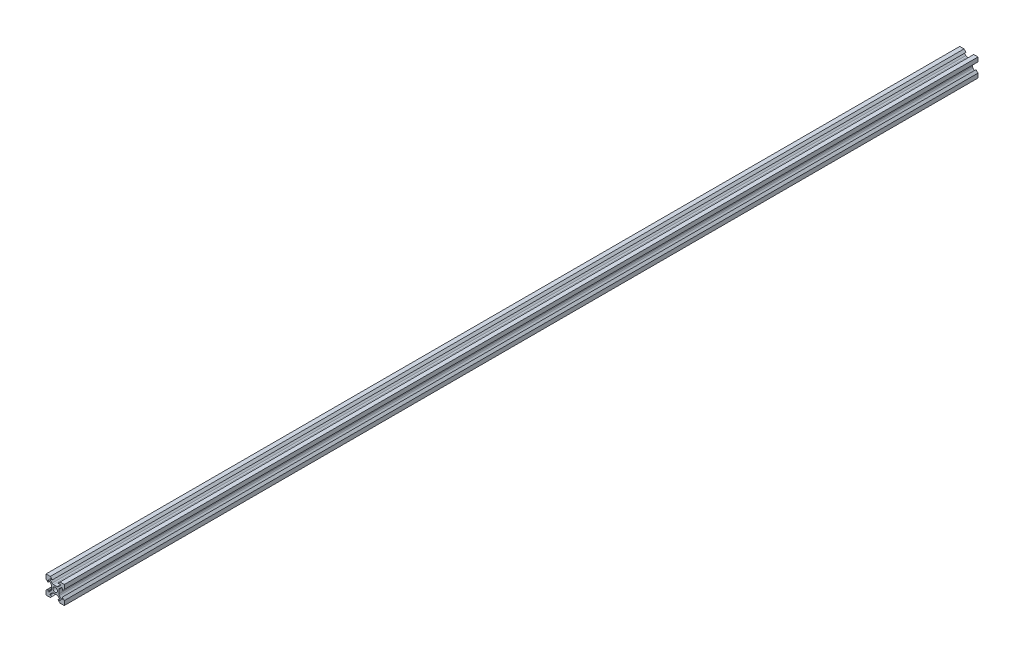
SolidWorks part; units mm, degrees
ref_plane "Front Plane" through (0, 0, 0) normal (0, 0, 1) x (1, 0, 0)
ref_plane "Top Plane" through (0, 0, 0) normal (0, 1, 0) x (1, 0, 0)
ref_plane "Right Plane" through (0, 0, 0) normal (1, 0, 0) x (0, 0, -1)
sketch "Sketch1" plane through (0, 0, 0) normal (0, 0, 1) x (1, 0, 0)
  line L0 (0, -10) -> (0, 10) construction
  line L1 (-10, 10) -> (10, 10) construction
  line L2 (-10, 10) -> (-10, -10) construction
  line L3 (-10, -10) -> (10, -10) construction
  line L4 (10, 10) -> (10, -10) construction
  line L5 (-10, 10) -> (10, -10) construction
  line L6 (-10, -10) -> (10, 10) construction
  line L7 (-10, 0) -> (10, 0) construction
  line L8 (-4, 0) -> (-4, 1.8988)
  line L9 (-4.5858, 3.313) -> (-6.8263, 5.5536)
  line L10 (-7.1799, 5.7) -> (-7.3, 5.7)
  line L11 (-7.8, 5.2) -> (-7.8, 3.1)
  line L12 (-7.8, 3.1) -> (-10, 5.3)
  line L13 (-10, 5.3) -> (-10, 10)
  line L14 (0, 4) -> (-1.8988, 4)
  line L15 (-3.313, 4.5858) -> (-5.5536, 6.8263)
  line L16 (-5.7, 7.1799) -> (-5.7, 7.3)
  line L17 (-5.2, 7.8) -> (-3.1, 7.8)
  line L18 (-3.1, 7.8) -> (-5.3, 10)
  line L19 (-5.3, 10) -> (-10, 10)
  line L20 (5.3, 10) -> (10, 10)
  line L21 (3.1, 7.8) -> (5.3, 10)
  line L22 (5.2, 7.8) -> (3.1, 7.8)
  line L23 (5.7, 7.1799) -> (5.7, 7.3)
  line L24 (3.313, 4.5858) -> (5.5536, 6.8263)
  line L25 (0, 4) -> (1.8988, 4)
  line L26 (10, -5.3) -> (10, -10)
  line L27 (7.8, -3.1) -> (10, -5.3)
  line L28 (7.8, -5.2) -> (7.8, -3.1)
  line L29 (7.1799, -5.7) -> (7.3, -5.7)
  line L30 (4.5858, -3.313) -> (6.8263, -5.5536)
  line L31 (4, 0) -> (4, -1.8988)
  line L32 (-5.3, -10) -> (-10, -10)
  line L33 (-3.1, -7.8) -> (-5.3, -10)
  line L34 (-5.2, -7.8) -> (-3.1, -7.8)
  line L35 (-5.7, -7.1799) -> (-5.7, -7.3)
  line L36 (-3.313, -4.5858) -> (-5.5536, -6.8263)
  line L37 (0, -4) -> (-1.8988, -4)
  line L38 (10, 5.3) -> (10, 10)
  line L39 (7.8, 3.1) -> (10, 5.3)
  line L40 (7.8, 5.2) -> (7.8, 3.1)
  line L41 (7.1799, 5.7) -> (7.3, 5.7)
  line L42 (4.5858, 3.313) -> (6.8263, 5.5536)
  line L43 (4, 0) -> (4, 1.8988)
  line L44 (5.3, -10) -> (10, -10)
  line L45 (3.1, -7.8) -> (5.3, -10)
  line L46 (5.2, -7.8) -> (3.1, -7.8)
  line L47 (5.7, -7.1799) -> (5.7, -7.3)
  line L48 (3.313, -4.5858) -> (5.5536, -6.8263)
  line L49 (0, -4) -> (1.8988, -4)
  line L50 (-10, -5.3) -> (-10, -10)
  line L51 (-7.8, -3.1) -> (-10, -5.3)
  line L52 (-7.8, -5.2) -> (-7.8, -3.1)
  line L53 (-7.1799, -5.7) -> (-7.3, -5.7)
  line L54 (-4.5858, -3.313) -> (-6.8263, -5.5536)
  line L55 (-4, 0) -> (-4, -1.8988)
  circle A0 centre (0, 0) radius 2.5
  arc A1 (-7.3, 5.7) -> (-7.8, 5.2) centre (-7.3, 5.2) ccw
  arc A2 (-6.8263, 5.5536) -> (-7.1799, 5.7) centre (-7.1799, 5.2) ccw
  arc A3 (-4, 1.8988) -> (-4.5858, 3.313) centre (-6, 1.8988) ccw
  arc A4 (-1.8988, 4) -> (-3.313, 4.5858) centre (-1.8988, 6) cw
  arc A5 (-5.5536, 6.8263) -> (-5.7, 7.1799) centre (-5.2, 7.1799) cw
  arc A6 (-5.7, 7.3) -> (-5.2, 7.8) centre (-5.2, 7.3) cw
  arc A7 (5.7, 7.3) -> (5.2, 7.8) centre (5.2, 7.3) ccw
  arc A8 (5.5536, 6.8263) -> (5.7, 7.1799) centre (5.2, 7.1799) ccw
  arc A9 (1.8988, 4) -> (3.313, 4.5858) centre (1.8988, 6) ccw
  arc A10 (7.3, -5.7) -> (7.8, -5.2) centre (7.3, -5.2) ccw
  arc A11 (6.8263, -5.5536) -> (7.1799, -5.7) centre (7.1799, -5.2) ccw
  arc A12 (4, -1.8988) -> (4.5858, -3.313) centre (6, -1.8988) ccw
  arc A13 (-5.7, -7.3) -> (-5.2, -7.8) centre (-5.2, -7.3) ccw
  arc A14 (-5.5536, -6.8263) -> (-5.7, -7.1799) centre (-5.2, -7.1799) ccw
  arc A15 (-1.8988, -4) -> (-3.313, -4.5858) centre (-1.8988, -6) ccw
  arc A16 (7.3, 5.7) -> (7.8, 5.2) centre (7.3, 5.2) cw
  arc A17 (6.8263, 5.5536) -> (7.1799, 5.7) centre (7.1799, 5.2) cw
  arc A18 (4, 1.8988) -> (4.5858, 3.313) centre (6, 1.8988) cw
  arc A19 (5.7, -7.3) -> (5.2, -7.8) centre (5.2, -7.3) cw
  arc A20 (5.5536, -6.8263) -> (5.7, -7.1799) centre (5.2, -7.1799) cw
  arc A21 (1.8988, -4) -> (3.313, -4.5858) centre (1.8988, -6) cw
  arc A22 (-7.3, -5.7) -> (-7.8, -5.2) centre (-7.3, -5.2) cw
  arc A23 (-6.8263, -5.5536) -> (-7.1799, -5.7) centre (-7.1799, -5.2) cw
  arc A24 (-4, -1.8988) -> (-4.5858, -3.313) centre (-6, -1.8988) cw
  dimension "D1" = 5
  dimension "D9" = 0.5
  dimension "D10" = 2
  dimension "D2" = 20
  dimension "D3" = 20
  dimension "D4" = 5.3
  dimension "D5" = 5.7
  dimension "D6" = 0.9
  dimension "D7" = 3.1
  dimension "D8" = 6
  dimension "D11" = 4
  dimension "D12" = 4
extrude "Boss-Extrude2" add sketch "Sketch1" along normal blind 1000
